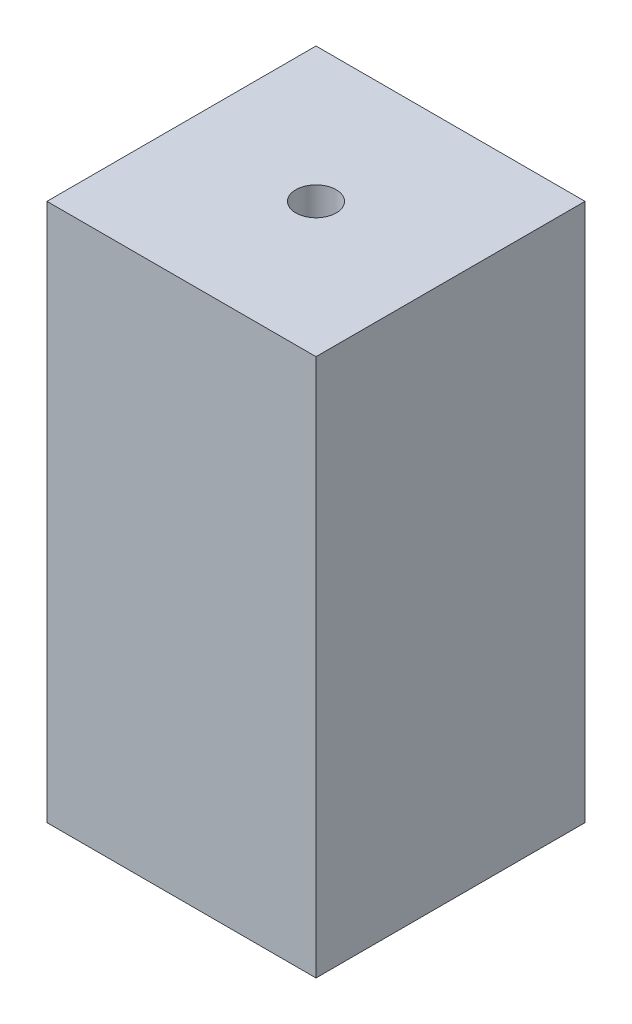
SolidWorks part; units mm, degrees
ref_plane "Front Plane" through (0, 0, 0) normal (0, 0, 1) x (1, 0, 0)
ref_plane "Top Plane" through (0, 0, 0) normal (0, 1, 0) x (1, 0, 0)
ref_plane "Right Plane" through (0, 0, 0) normal (1, 0, 0) x (0, 0, -1)
sketch "Sketch1" plane through (0, 0, 0) normal (0, 1, 0) x (1, 0, 0)
  line L1 (0, 0) -> (10, 0)
  line L2 (0, 0) -> (0, 10)
  line L3 (0, 10) -> (10, 10)
  line L4 (10, 0) -> (10, 10)
  dimension "D1" = 10
  dimension "D2" = 10
extrude "Boss-Extrude1" add sketch "Sketch1" along normal blind 20
sketch "Sketch2" plane through (0, 20, 0) normal (0, 1, 0) x (1, 0, 0)
  line L0 (10, 10) -> (0, 0) construction
  circle A1 centre (5, 5) radius 0.75
  dimension "D1" = 1.5
extrude "Cut-Extrude2" cut sketch "Sketch2" against normal blind 21 contours A1
